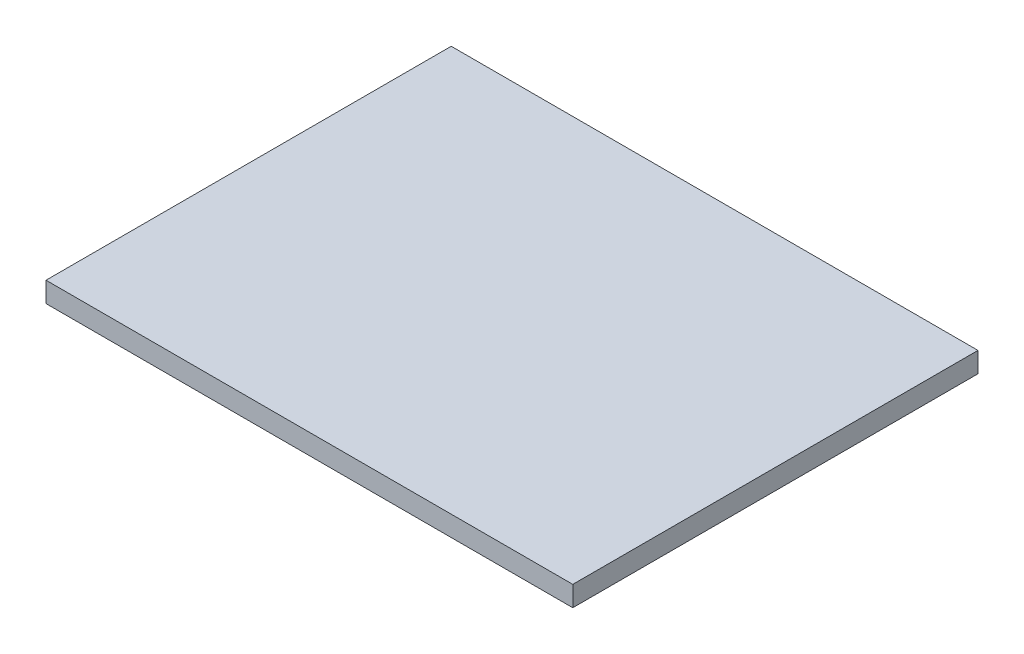
SolidWorks part; units mm, degrees
ref_plane "Front Plane" through (0, 0, 0) normal (0, 0, 1) x (1, 0, 0)
ref_plane "Top Plane" through (0, 0, 0) normal (0, 1, 0) x (1, 0, 0)
ref_plane "Right Plane" through (0, 0, 0) normal (1, 0, 0) x (0, 0, -1)
sketch "Sketch1" plane through (0, 0, 0) normal (0, 1, 0) x (1, 0, 0)
  line L1 (-60, -45) -> (60, -45)
  line L2 (-60, -45) -> (-60, 45)
  line L3 (-60, 45) -> (60, 45)
  line L4 (60, -45) -> (60, 45)
  line L5 (-60, -45) -> (60, 45) construction
  line L6 (-60, 45) -> (60, -45) construction
  point P0 (0, 0)
  dimension "D1" = 120
  dimension "D2" = 90
extrude "Boss-Extrude1" add sketch "Sketch1" along normal blind 5
sketch "Sketch2" plane through (0, 5, 0) normal (0, 1, 0) x (1, 0, 0)
  line L0 (60, 45) -> (-60, 45) construction
  line L1 (-65, -50) -> (65, -50)
  line L2 (-65, -50) -> (-65, 50)
  line L3 (-65, 50) -> (65, 50)
  line L4 (65, -50) -> (65, 50)
  line L5 (-65, -50) -> (65, 50) construction
  line L6 (-65, 50) -> (65, -50) construction
  line L7 (-60, 45) -> (-60, -45) construction
  point P0 (0, 0)
  dimension "D1" = 5
  dimension "D2" = 5
extrude "Boss-Extrude2" add sketch "Sketch2" along normal blind 5
